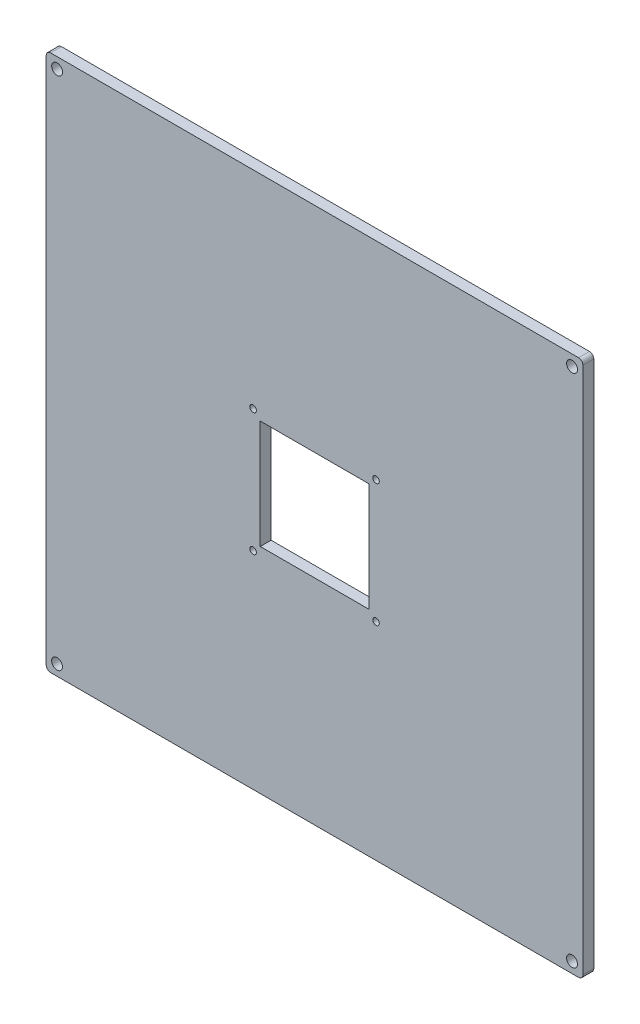
SolidWorks part; units mm, degrees
material "Glass"
ref_plane "Front Plane" through (0, 0, 0) normal (0, 0, 1) x (1, 0, 0)
ref_plane "Top Plane" through (0, 0, 0) normal (0, 1, 0) x (1, 0, 0)
ref_plane "Right Plane" through (0, 0, 0) normal (1, 0, 0) x (0, 0, -1)
sketch "Sketch1" plane through (0, 0, 0) normal (0, 0, 1) x (1, 0, 0)
  line L0 (-123.5, 121.5) -> (-123.5, -121.5)
  line L1 (-121.5, -123.5) -> (121.5, -123.5)
  line L2 (123.5, -121.5) -> (123.5, 121.5)
  line L3 (121.5, 123.5) -> (-121.5, 123.5)
  line L4 (0, 0) -> (0, 144.9076) construction
  line L5 (0, 0) -> (173.8049, 0) construction
  arc A0 (-123.5, -121.5) -> (-121.5, -123.5) centre (-121.5, -121.5) ccw
  arc A1 (121.5, -123.5) -> (123.5, -121.5) centre (121.5, -121.5) ccw
  arc A2 (123.5, 121.5) -> (121.5, 123.5) centre (121.5, 121.5) ccw
  arc A3 (-123.5, 121.5) -> (-121.5, 123.5) centre (-121.5, 121.5) cw
  circle A4 centre (-118.5, 118.5) radius 2.5
  circle A8 centre (118.5, 118.5) radius 2.5
  circle A9 centre (118.5, -118.5) radius 2.5
  circle A10 centre (-118.5, -118.5) radius 2.5
  dimension "D5" = 2
  dimension "D6" = 5
  dimension "D1" = 247
  dimension "D2" = 123.5
  dimension "D3" = 123.5
  dimension "D4" = 247
  dimension "D10" = 5
  dimension "D11" = 5
extrude "Boss-Extrude1" add sketch "Sketch1" along normal blind 5
sketch "Sketch2" plane through (0, 0, 0) normal (0, 0, -1) x (-1, 0, 0)
  line L0 (-25, 25) -> (-25, -25)
  line L1 (-25, -25) -> (25, -25)
  line L2 (25, -25) -> (25, 25)
  line L3 (25, 25) -> (-25, 25)
  line L4 (0, 0) -> (74.833, 0) construction
  line L5 (0, 0) -> (55.9239, 55.9239) construction
  line L6 (0, 0) -> (0, 65.9297) construction
  circle A0 centre (28.2843, 28.2843) radius 1.5
  circle A1 centre (28.2843, -28.2843) radius 1.5
  circle A2 centre (-28.2843, -28.2843) radius 1.5
  circle A3 centre (-28.2843, 28.2843) radius 1.5
  dimension "D7" = 3
  dimension "D1" = 25
  dimension "D2" = 25
  dimension "D3" = 25
  dimension "D4" = 25
  dimension "D5" = 45
  dimension "D6" = 40
extrude "Cut-Extrude1" cut sketch "Sketch2" against normal blind 5
